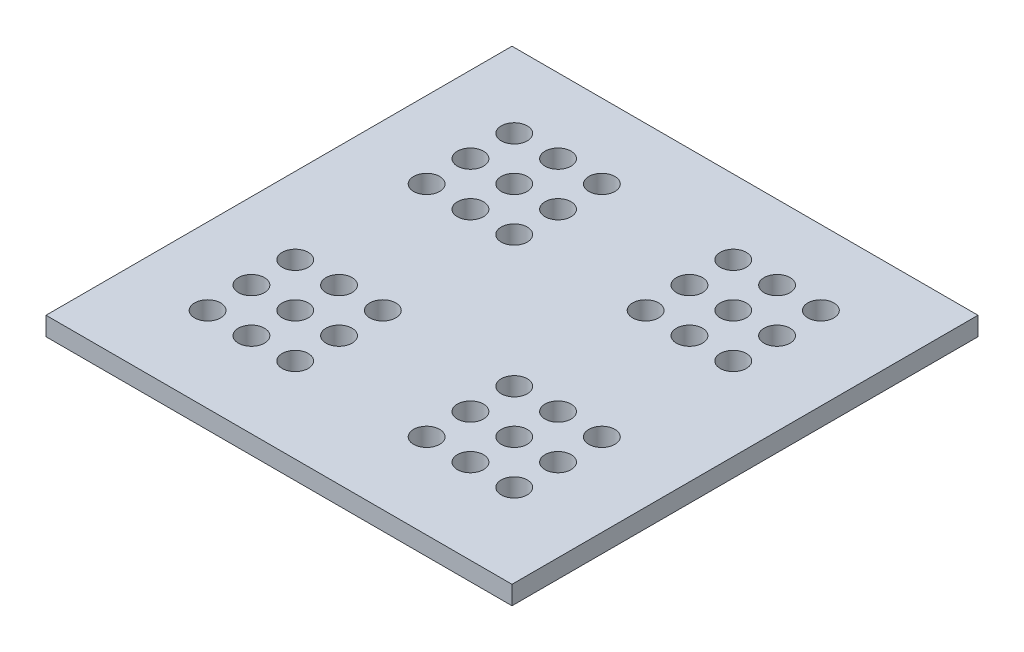
SolidWorks part; units mm, degrees
ref_plane "Front Plane" through (0, 0, 0) normal (0, 0, 1) x (1, 0, 0)
ref_plane "Top Plane" through (0, 0, 0) normal (0, 1, 0) x (1, 0, 0)
ref_plane "Right Plane" through (0, 0, 0) normal (1, 0, 0) x (0, 0, -1)
sketch "Sketch1" plane through (0, 0, 0) normal (0, 1, 0) x (1, 0, 0)
  line L1 (-12.5, 12.5) -> (12.5, 12.5)
  line L2 (-12.5, 12.5) -> (-12.5, -12.5)
  line L3 (-12.5, -12.5) -> (12.5, -12.5)
  line L4 (12.5, 12.5) -> (12.5, -12.5)
  circle A0 centre (-8.39, 8.51) radius 0.7
  circle A1 centre (-6.04, 8.51) radius 0.7
  circle A2 centre (-3.69, 8.51) radius 0.7
  circle A5 centre (3.36, 8.51) radius 0.7
  circle A6 centre (5.71, 8.51) radius 0.7
  circle A7 centre (8.06, 8.51) radius 0.7
  circle A8 centre (-6.04, 6.16) radius 0.7
  circle A9 centre (-3.69, 6.16) radius 0.7
  circle A12 centre (3.36, 6.16) radius 0.7
  circle A13 centre (5.71, 6.16) radius 0.7
  circle A14 centre (8.06, 6.16) radius 0.7
  circle A15 centre (-6.04, 3.81) radius 0.7
  circle A16 centre (-3.69, 3.81) radius 0.7
  circle A19 centre (3.36, 3.81) radius 0.7
  circle A20 centre (5.71, 3.81) radius 0.7
  circle A21 centre (8.06, 3.81) radius 0.7
  circle A29 centre (-8.39, 6.16) radius 0.7
  circle A30 centre (-8.39, 3.81) radius 0.7
  circle A40 centre (-6.04, -3.24) radius 0.7
  circle A41 centre (-3.69, -3.24) radius 0.7
  circle A44 centre (3.36, -3.24) radius 0.7
  circle A45 centre (5.71, -3.24) radius 0.7
  circle A46 centre (8.06, -3.24) radius 0.7
  circle A47 centre (-6.04, -5.59) radius 0.7
  circle A48 centre (-3.69, -5.59) radius 0.7
  circle A51 centre (3.36, -5.59) radius 0.7
  circle A52 centre (5.71, -5.59) radius 0.7
  circle A53 centre (8.06, -5.59) radius 0.7
  circle A54 centre (-6.04, -7.94) radius 0.7
  circle A55 centre (-3.69, -7.94) radius 0.7
  circle A58 centre (3.36, -7.94) radius 0.7
  circle A59 centre (5.71, -7.94) radius 0.7
  circle A60 centre (8.06, -7.94) radius 0.7
  circle A61 centre (-8.39, -3.24) radius 0.7
  circle A62 centre (-8.39, -5.59) radius 0.7
  circle A63 centre (-8.39, -7.94) radius 0.7
  circle A64 centre (-1.34, 8.51) radius 0.7 [skipped]
  circle A65 centre (-1.34, 6.16) radius 0.7 [skipped]
  circle A66 centre (-1.34, 3.81) radius 0.7 [skipped]
  circle A67 centre (-1.34, 1.46) radius 0.7 [skipped]
  circle A68 centre (1.01, 8.51) radius 0.7 [skipped]
  circle A69 centre (1.01, 6.16) radius 0.7 [skipped]
  circle A70 centre (1.01, 3.81) radius 0.7 [skipped]
  circle A71 centre (1.01, 1.46) radius 0.7 [skipped]
  circle A72 centre (-6.04, 1.46) radius 0.7 [skipped]
  circle A73 centre (-3.69, 1.46) radius 0.7 [skipped]
  circle A74 centre (3.36, 1.46) radius 0.7 [skipped]
  circle A75 centre (5.71, 1.46) radius 0.7 [skipped]
  circle A76 centre (8.06, 1.46) radius 0.7 [skipped]
  circle A77 centre (-8.39, 1.46) radius 0.7 [skipped]
  circle A78 centre (-8.39, -0.89) radius 0.7 [skipped]
  circle A79 centre (-6.04, -0.89) radius 0.7 [skipped]
  circle A80 centre (-3.69, -0.89) radius 0.7 [skipped]
  circle A81 centre (3.36, -0.89) radius 0.7 [skipped]
  circle A82 centre (5.71, -0.89) radius 0.7 [skipped]
  circle A83 centre (8.06, -0.89) radius 0.7 [skipped]
  dimension "D5" = 8
  dimension "D7" = 3.99
  dimension "D1" = 12.5
  dimension "D2" = 25
  dimension "D3" = 12.5
  dimension "D4" = 25
  dimension "D8" = 4.11
  dimension "D6" = 4
  dimension "D9" = 2
extrude "Boss-Extrude2" add sketch "Sketch1" along normal blind 1
